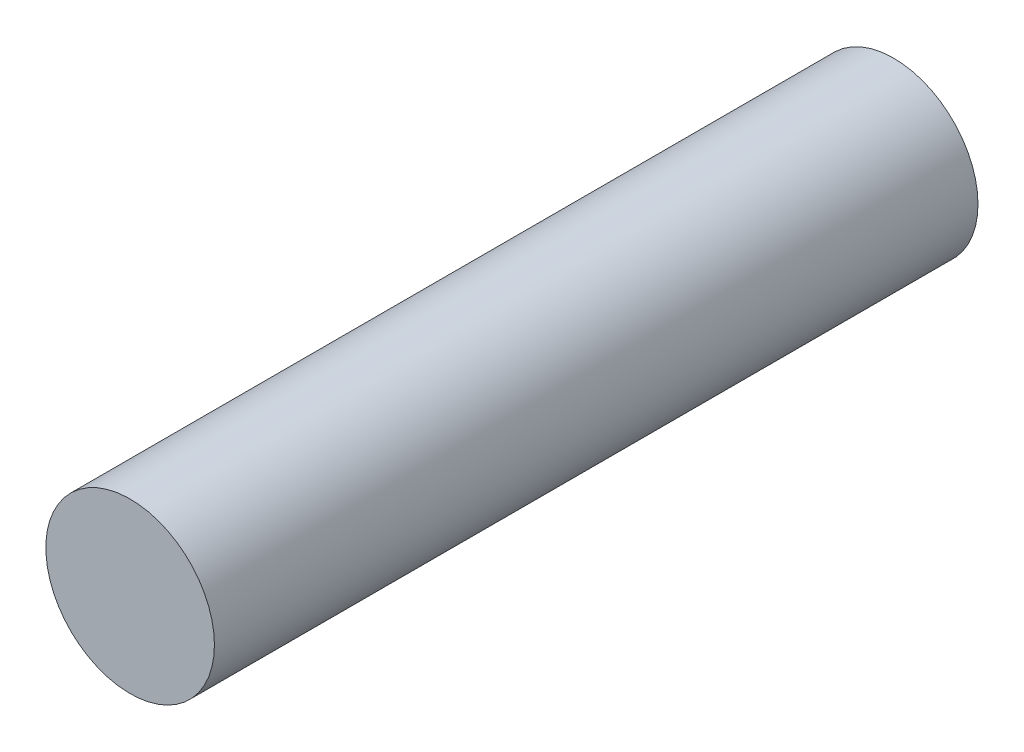
SolidWorks part; units mm, degrees
ref_plane "Front Plane" through (0, 0, 0) normal (0, 0, 1) x (1, 0, 0)
ref_plane "Top Plane" through (0, 0, 0) normal (0, 1, 0) x (1, 0, 0)
ref_plane "Right Plane" through (0, 0, 0) normal (1, 0, 0) x (0, 0, -1)
sketch "Sketch1" plane through (0, 0, 0) normal (0, 0, 1) x (1, 0, 0)
  circle A0 centre (0, 0) radius 39.2557
  dimension "D2" = 78.5114
extrude "Boss-Extrude1" add sketch "Sketch1" along normal mid plane 355.6
equation "\"AIRFRAME_OD\"= 5.15in"
equation "\"AIRFRAME_ID\"= 5.00in"
equation "\"FLAT_T\"= 0.125in"
equation "\"NOSE_EXP_L\"= 27in"
equation "\"NOSE_SHOULDER_L\"= 5in"
equation "\"MAIN_L\"= 30in"
equation "\"RECO_COUP_L\"= 10in"
equation "\"RECO_SWITCH_L\"= 2in"
equation "\"DROGUE_L\"= 20in"
equation "\"ATS_FORE_COUP_L\"= 5.5in"
equation "\"ATS_AFT_COUP_L\"= 4.5in"
equation "\"LOWER_L\"= 30in"
equation "\"FIN_N\"= 4"
equation "\"CR_AFT_X\"= 0.5in"
equation "\"CR_FORE_X\"= 9.25in"
equation "\"D2@Sketch1\"=\"MOTOR_OD\""
equation "\"D1@Boss-Extrude1\"=\"MOTOR_L\""
equation "\"FIN_ROOT\"= 8in"
equation "\"FIN_X\"= 0.75in"
equation "\"MOTOR_OD\"= 3.091in"
equation "\"MOTOR_ID\"= 3.00in"
equation "\"COUPLER_OD\"= 4.998in"
equation "\"COUPLER_ID\"= 4.88in"
equation "\"RECO_ROD_X\"= 3.5in"
equation "\"ATS_ROD_X\"= 3.75in"
equation "\"MOTOR_L\"= 14in"
equation "\"MOTOR_LOWER_X\"= 2in"
